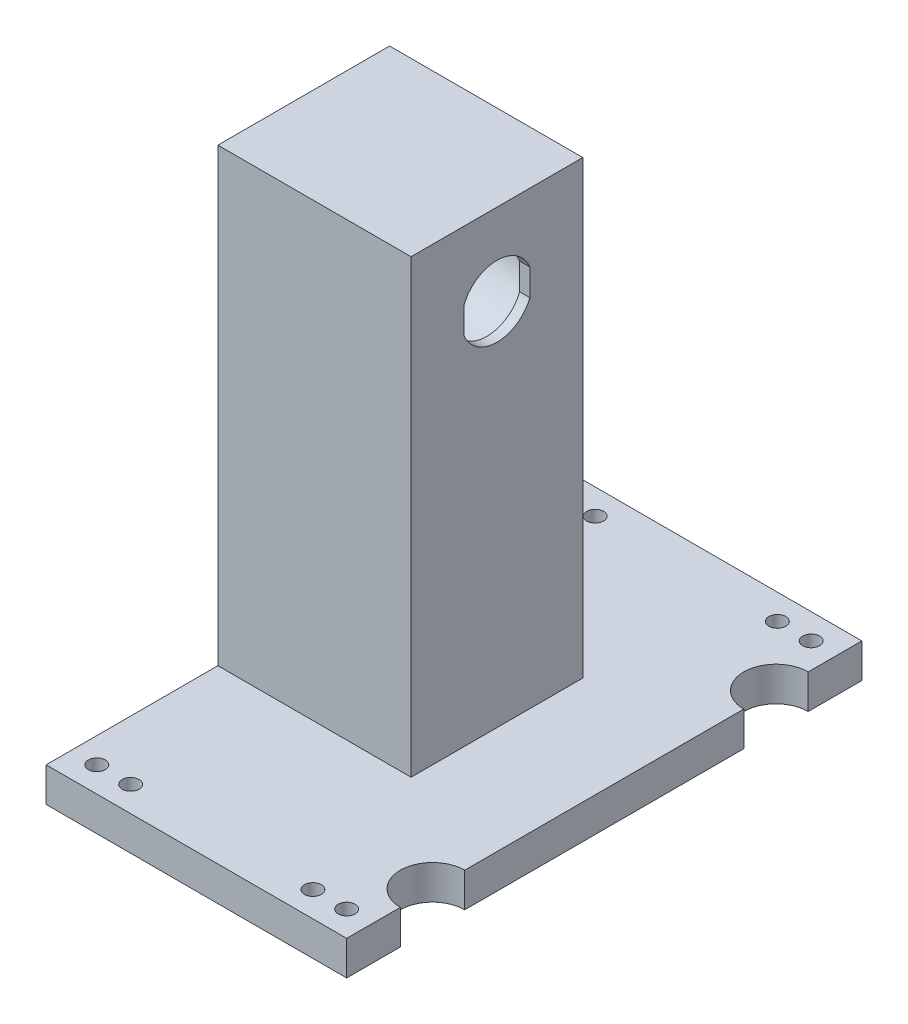
SolidWorks part; units mm, degrees
ref_plane "Front Plane" through (0, 0, 0) normal (0, 0, 1) x (1, 0, 0)
ref_plane "Top Plane" through (0, 0, 0) normal (0, 1, 0) x (1, 0, 0)
ref_plane "Right Plane" through (0, 0, 0) normal (1, 0, 0) x (0, 0, -1)
sketch "Sketch2" plane through (0, 0, 0) normal (0, 1, 0) x (1, 0, 0)
  line L1 (-35.56, 56.5856) -> (53.34, 56.5856)
  line L2 (-35.56, 56.5856) -> (-35.56, -95.8144)
  line L3 (-35.56, -95.8144) -> (53.34, -95.8144)
  line L4 (53.34, 56.5856) -> (53.34, -95.8144)
  dimension "3.5" = 88.9
  dimension "D2" = 152.4
extrude "Boss-Extrude1" add sketch "Sketch2" along normal blind 10.16
sketch "Sketch5" plane through (0, 10.16, 0) normal (0, 1, 0) x (1, 0, 0)
  line L0 (-35.56, 56.5856) -> (-35.56, -95.8144) construction
  line L1 (-35.56, -45.0144) -> (21.59, -45.0144)
  line L2 (-35.56, -45.0144) -> (-35.56, 5.7856)
  line L3 (-35.56, 5.7856) -> (21.59, 5.7856)
  line L4 (21.59, -45.0144) -> (21.59, 5.7856)
  line L7 (-35.56, -95.8144) -> (53.34, -95.8144) construction
  dimension "D1" = 50.8
  dimension "D2" = 57.15
  dimension "D3" = 50.8
extrude "Boss-Extrude2" add sketch "Sketch5" along normal blind 133.35
sketch "Sketch6" plane through (0, 10.16, 0) normal (0, 1, 0) x (1, 0, 0)
  line L0 (-35.56, -95.8144) -> (53.34, -95.8144) construction
  line L1 (53.34, 56.5856) -> (-35.56, 56.5856) construction
  line L2 (-35.56, -45.0144) -> (-35.56, -95.8144) construction
  line L3 (53.34, -95.8144) -> (53.34, 56.5856) construction
  circle A0 centre (35.84, -88.3144) radius 2.5
  circle A1 centre (45.84, -88.3144) radius 2.5
  circle A2 centre (-28.06, -88.3144) radius 2.5
  circle A3 centre (-18.06, -88.3144) radius 2.5
  circle A4 centre (-28.06, 49.0856) radius 2.5
  circle A5 centre (-18.06, 49.0856) radius 2.5
  circle A6 centre (35.84, 49.0856) radius 2.5
  circle A7 centre (45.84, 49.0856) radius 2.5
  dimension "D1" = 5
  dimension "D2" = 10
  dimension "D3" = 10
  dimension "D4" = 7.5
  dimension "D5" = 7.5
  dimension "D6" = 7.5
  dimension "D7" = 7.5
extrude "Cut-Extrude1" cut sketch "Sketch6" against normal through all
sketch "Sketch7" plane through (21.59, 0, 0) normal (1, 0, 0) x (0, 0, -1)
  line L0 (-45.0144, 10.16) -> (5.7856, 10.16) construction
  line L1 (5.7856, 143.51) -> (5.7856, 10.16) construction
  circle A0 centre (-19.6144, 119.38) radius 10.5
  dimension "D2" = 21
  dimension "D1" = 109.22
  dimension "D3" = 25.4
extrude "Cut-Extrude2" cut sketch "Sketch7" against normal through all
sketch "Sketch8" plane through (-35.56, 0, 0) normal (-1, 0, 0) x (0, 0, 1)
  circle A0 centre (19.6144, 119.38) radius 16.5
  circle A1 centre (19.6144, 119.38) radius 10.5 construction
  point P3 (19.6144, 135.88)
  point P4 (19.6144, 129.88)
  dimension "D1" = 33
extrude "Cut-Extrude3" cut sketch "Sketch8" against normal blind 54.15
sketch "Sketch9" plane through (-35.56, 0, 0) normal (-1, 0, 0) x (0, 0, 1)
  circle A0 centre (19.6144, 119.38) radius 19.5
  dimension "D1" = 39
extrude "Cut-Extrude4" cut sketch "Sketch9" against normal blind 16.51
sketch "Sketch10" plane through (21.59, 0, 0) normal (1, 0, 0) x (0, 0, -1)
  line L0 (-29.3484, 123.317) -> (-29.3484, 115.443)
  line L2 (-9.8805, 115.443) -> (-9.8805, 123.317)
  circle A0 centre (-19.6144, 119.38) radius 10.5 construction
  arc A1 (-29.3484, 123.317) -> (-29.3484, 115.443) centre (-19.6144, 119.38) ccw
  arc A2 (-9.8805, 123.317) -> (-9.8805, 115.443) centre (-19.6144, 119.38) cw
  dimension "D1" = 7.874
extrude "Boss-Extrude3" add sketch "Sketch10" against normal up to surface (3 mm away) up to face at (18.59, 119.38, 36.1144)
sketch "Sketch12" plane through (0, 10.16, 0) normal (0, 1, 0) x (1, 0, 0)
  line L0 (-35.56, -95.8144) -> (53.34, -95.8144) construction
  line L1 (53.34, 56.5856) -> (-35.56, 56.5856) construction
  line L2 (53.34, -95.8144) -> (53.34, 56.5856) construction
  circle A0 centre (53.34, -70.4144) radius 9.525
  circle A1 centre (53.34, 31.1856) radius 9.525
  dimension "D1" = 19.05
  dimension "D2" = 25.4
  dimension "D3" = 25.4
  dimension "D4" = 0
extrude "Cut-Extrude6" cut sketch "Sketch12" against normal blind 12.7
